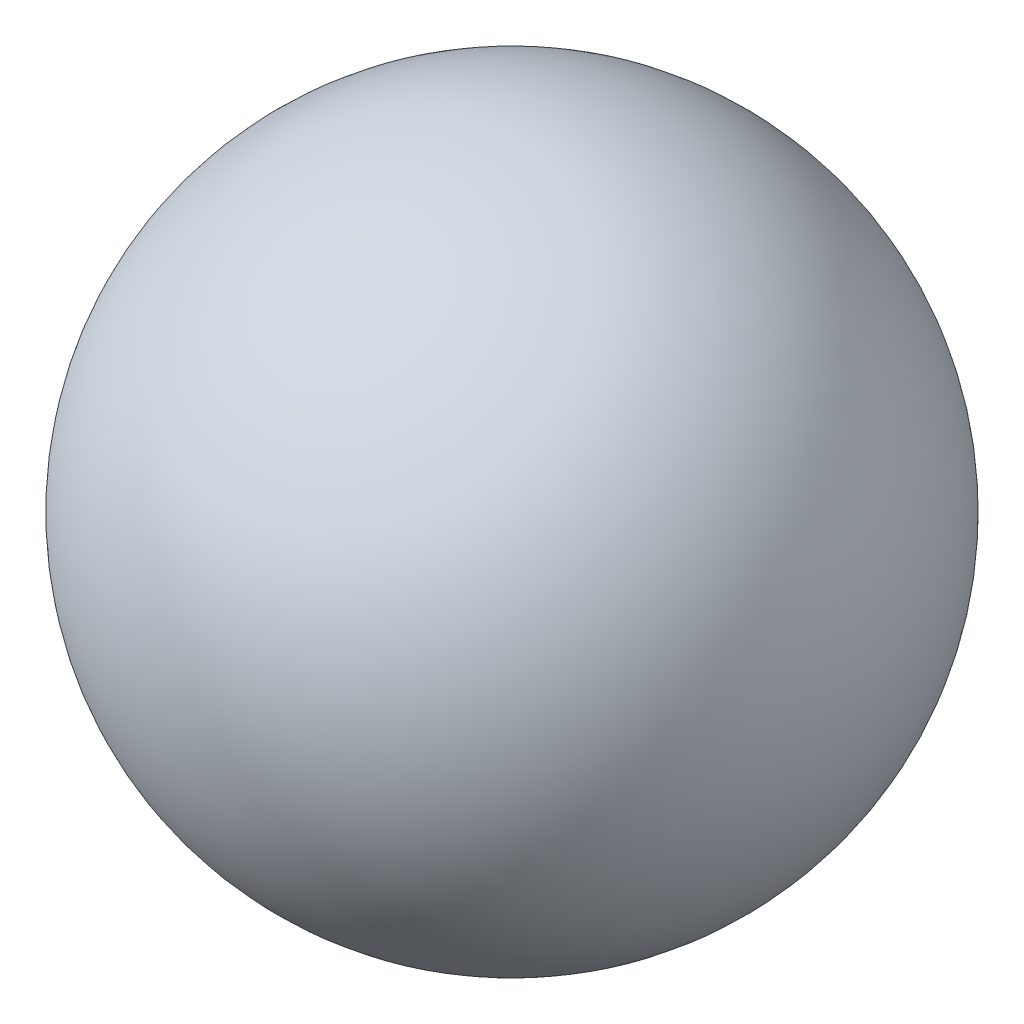
SolidWorks part; units mm, degrees
material "BUTYL"
ref_plane "Front Plane" through (0, 0, 0) normal (0, 0, 1) x (1, 0, 0)
ref_plane "Top Plane" through (0, 0, 0) normal (0, 1, 0) x (1, 0, 0)
ref_plane "Right Plane" through (0, 0, 0) normal (1, 0, 0) x (0, 0, -1)
sketch "Sketch1" plane through (0, 0, 0) normal (0, 0, 1) x (1, 0, 0)
  line L0 (0, -165.1) -> (0, 165.1)
  arc A0 (0, 165.1) -> (0, -165.1) centre (0, 0) cw
  dimension "D1" = 330.2
revolve "Revolve2" add sketch "Sketch1" angle 360 about L0
